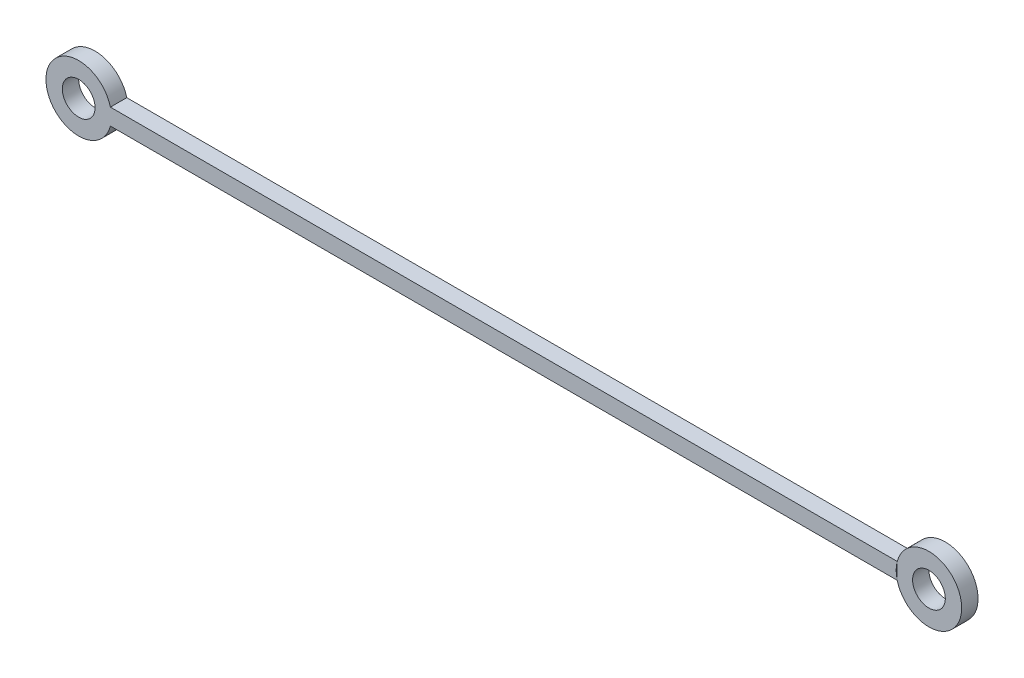
SolidWorks part; units mm, degrees
material "Plain Carbon Steel"
ref_plane "Front Plane" through (0, 0, 0) normal (0, 0, 1) x (1, 0, 0)
ref_plane "Top Plane" through (0, 0, 0) normal (0, 1, 0) x (1, 0, 0)
ref_plane "Right Plane" through (0, 0, 0) normal (1, 0, 0) x (0, 0, -1)
sketch "Sketch2" plane through (0, 0, 0) normal (0, 0, 1) x (1, 0, 0)
  line L0 (-3.873, 1) -> (-103.873, 1)
  line L1 (-3.873, -1) -> (-103.873, -1)
  line L2 (-103.873, 1) -> (-103.873, -1)
  line L3 (-3.873, 1) -> (-3.873, -1)
  circle A0 centre (0, 0) radius 2
  circle A1 centre (0, 0) radius 4
  circle A2 centre (-103.873, 0) radius 2
  circle A3 centre (-103.873, 0) radius 4
  dimension "D1" = 4
  dimension "D6" = 4
  dimension "D7" = 2
  dimension "D3" = 100
  dimension "D4" = 2
  dimension "D5" = 1
  dimension "D2" = 2
extrude "Boss-Extrude1" add sketch "Sketch2" along normal blind 2 contours L0 A3 L1 A2 | A3 L1 A1 L0 | L1 A3 L0 A2 | L3 A1 A0
